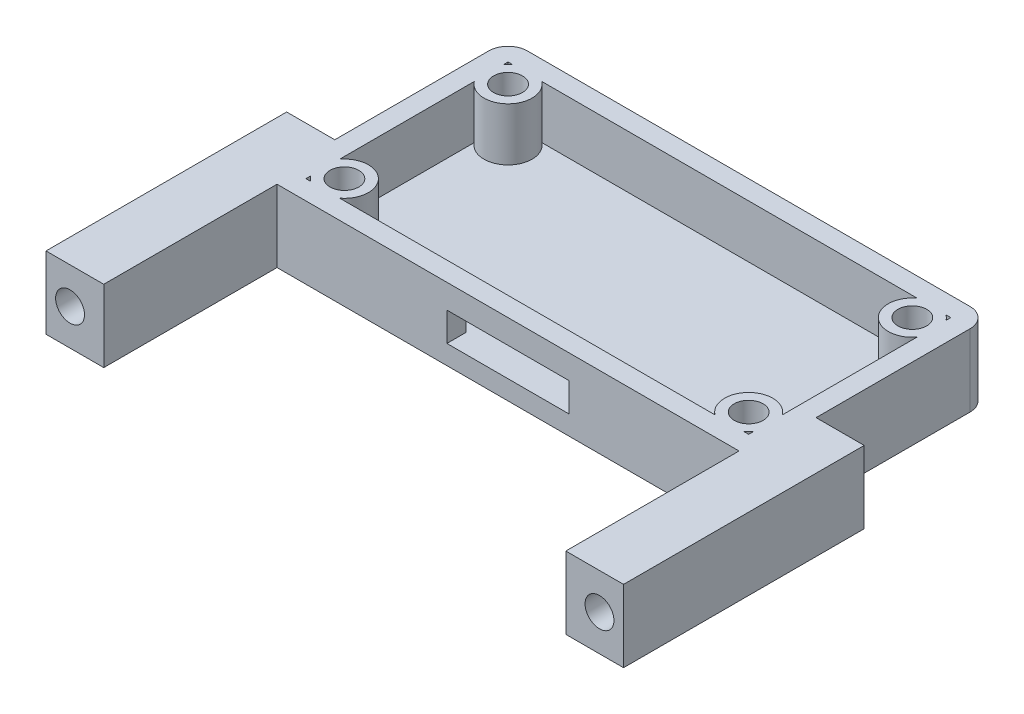
SolidWorks part; units mm, degrees
ref_plane "前视基准面" through (0, 0, 0) normal (0, 0, 1) x (1, 0, 0)
ref_plane "上视基准面" through (0, 0, 0) normal (0, 1, 0) x (1, 0, 0)
ref_plane "右视基准面" through (0, 0, 0) normal (1, 0, 0) x (0, 0, -1)
other "Configuration Table"
sketch "草图1" plane through (0, 0, 0) normal (0, 1, 0) x (1, 0, 0)
  line L1 (-23, 12.5) -> (23, 12.5)
  line L2 (-25, 10.5) -> (-25, -10.5)
  line L3 (-23, -12.5) -> (23, -12.5)
  line L4 (25, 10.5) -> (25, -10.5)
  line L5 (-25, 12.5) -> (25, -12.5) construction
  line L6 (-25, -12.5) -> (25, 12.5) construction
  arc A0 (-23, 12.5) -> (-25, 10.5) centre (-23, 10.5) ccw
  arc A1 (25, 10.5) -> (23, 12.5) centre (23, 10.5) ccw
  arc A2 (-25, -10.5) -> (-23, -12.5) centre (-23, -10.5) ccw
  arc A3 (23, -12.5) -> (25, -10.5) centre (23, -10.5) ccw
  point P0 (0, 0)
  dimension "D3" = 4
  dimension "D4" = 4
  dimension "D5" = 4
  dimension "D6" = 4
  dimension "D1" = 50
  dimension "D2" = 25
extrude "凸台-拉伸1" add sketch "草图1" along normal blind 2
sketch "草图2" plane through (0, 2, 0) normal (0, 1, 0) x (1, 0, 0)
  line L0 (-25, 10.5) -> (-25, -10.5) construction
  line L1 (-23, 10.5) -> (23, 10.5)
  line L2 (-23, 10.5) -> (-23, -10.5)
  line L3 (-23, -10.5) -> (23, -10.5)
  line L4 (23, 10.5) -> (23, -10.5)
  line L5 (-23, 10.5) -> (23, -10.5) construction
  line L6 (-23, -10.5) -> (23, 10.5) construction
  line L8 (23, 12.5) -> (-23, 12.5) construction
  line L13 (-25, 10.5) -> (-25, -10.5)
  line L14 (-23, -12.5) -> (23, -12.5)
  line L15 (25, -10.5) -> (25, 10.5)
  line L16 (23, 12.5) -> (-23, 12.5)
  line L17 (-25, 10.5) -> (-25, -10.5)
  line L18 (-23, -12.5) -> (23, -12.5)
  line L19 (25, -10.5) -> (25, 10.5)
  line L20 (23, 12.5) -> (-23, 12.5)
  arc A4 (-23, 12.5) -> (-25, 10.5) centre (-23, 10.5) ccw
  arc A5 (-25, -10.5) -> (-23, -12.5) centre (-23, -10.5) ccw
  arc A6 (23, -12.5) -> (25, -10.5) centre (23, -10.5) ccw
  arc A7 (25, 10.5) -> (23, 12.5) centre (23, 10.5) ccw
  arc A8 (-23, 12.5) -> (-25, 10.5) centre (-23, 10.5) ccw
  arc A9 (-25, -10.5) -> (-23, -12.5) centre (-23, -10.5) ccw
  arc A10 (23, -12.5) -> (25, -10.5) centre (23, -10.5) ccw
  arc A11 (25, 10.5) -> (23, 12.5) centre (23, 10.5) ccw
  point P0 (0, 0)
  dimension "D1" = 2
  dimension "D2" = 2
  dimension "D3" = 0
extrude "凸台-拉伸2" add sketch "草图2" along normal blind 5.5
sketch "草图3" plane through (0, 2, 0) normal (0, 1, 0) x (1, 0, 0)
  line L0 (-23, 10.5) -> (-23, -10.5) construction
  line L1 (23, 10.5) -> (-23, 10.5) construction
  line L2 (23, -10.5) -> (23, 10.5) construction
  line L3 (-23, 10.5) -> (-23, -10.5) construction
  line L6 (-23, -10.5) -> (23, -10.5) construction
  line L7 (23, -10.5) -> (23, 10.5) construction
  circle A0 centre (-21, 8.5) radius 1.5
  circle A1 centre (-21, -8.5) radius 1.5
  circle A2 centre (21, -8.5) radius 1.5
  circle A3 centre (21, 8.5) radius 1.5
  circle A4 centre (-21, 8.5) radius 2.5
  circle A5 centre (21, 8.5) radius 2.5
  circle A6 centre (21, -8.5) radius 2.5
  circle A7 centre (-21, -8.5) radius 2.5
  dimension "D1" = 3
  dimension "D2" = 3
  dimension "D3" = 3
  dimension "D4" = 3
  dimension "D6" = 2
  dimension "D7" = 2
  dimension "D8" = 2
  dimension "D13" = 5
  dimension "D14" = 5
  dimension "D15" = 5
  dimension "D16" = 5
  dimension "D5" = 2
  dimension "D9" = 2
  dimension "D10" = 2
  dimension "D11" = 2
  dimension "D12" = 2
extrude "凸台-拉伸3" add sketch "草图3" along normal blind 5.5
sketch "草图4" plane through (0, 7.5, 0) normal (0, 1, 0) x (1, 0, 0)
  line L0 (19.5, 10.5) -> (-19.5, 10.5) construction
  line L1 (-23, 7) -> (-23, -7) construction
  line L2 (-19.5, -10.5) -> (19.5, -10.5) construction
  line L3 (-23, 7) -> (-23, -7) construction
  line L4 (23, -7) -> (23, 7) construction
  line L5 (19.5, 10.5) -> (-19.5, 10.5) construction
  line L6 (23, -7) -> (23, 7) construction
  circle A8 centre (-21.5, 9) radius 1.5
  circle A9 centre (-21.5, -9) radius 1.5
  circle A10 centre (21.5, 9) radius 1.5
  circle A11 centre (21.5, -9) radius 1.5
  dimension "D1" = 3
  dimension "D2" = 3
  dimension "D3" = 3
  dimension "D4" = 3
  dimension "D7" = 1.5
  dimension "D9" = 1.5
  dimension "D10" = 1.5
  dimension "D11" = 1.5
  dimension "D12" = 1.5
  dimension "D5" = 1.5
  dimension "D6" = 1.5
  dimension "D8" = 1.5
sketch "草图5" plane through (0, 0, 12.5) normal (0, 0, 1) x (1, 0, 0)
  line L0 (-23, 0) -> (23, 0) construction
  line L1 (-6.35, 2) -> (6.35, 2)
  line L2 (-6.35, 2) -> (-6.35, 5)
  line L3 (-6.35, 5) -> (6.35, 5)
  line L4 (6.35, 2) -> (6.35, 5)
  dimension "D1" = 12.7
  dimension "D2" = 2
  dimension "D3" = 3
  dimension "D4" = 6.35
extrude "切除-拉伸2" cut sketch "草图5" against normal up to next
sketch "草图6" plane through (0, 0, 0) normal (0, -1, 0) x (1, 0, 0)
  line L0 (23, 12.5) -> (30, 12.5)
  line L1 (30, 12.5) -> (30, 10.5)
  line L2 (30, 10.5) -> (25, 10.5)
  line L3 (25, 10.5) -> (23, 12.5)
  line L4 (-23, 12.5) -> (-30, 12.5)
  line L5 (-30, 12.5) -> (-30, 10.5)
  line L6 (-30, 10.5) -> (-25, 10.5)
  line L7 (-25, 10.5) -> (-23, 12.5)
  dimension "D1" = 7
  dimension "D2" = 7
extrude "凸台-拉伸4" add sketch "草图6" against normal up to surface (7.5 mm away)
sketch "草图7" plane through (0, 0, 10.5) normal (0, 0, -1) x (-1, 0, 0)
  line L0 (-30, 7.5) -> (-30, 0) construction
  line L1 (-25, 7.5) -> (-30, 7.5) construction
  line L2 (30, 7.5) -> (25, 7.5) construction
  line L4 (30, 7.5) -> (30, 0) construction
  circle A0 centre (-27.5, 3.75) radius 1.5
  circle A1 centre (27.5, 3.75) radius 1.5
  dimension "D5" = 3
  dimension "D6" = 3
  dimension "D1" = 2.5
  dimension "D2" = 3.75
  dimension "D3" = 3.75
  dimension "D4" = 2.5
extrude "切除-拉伸3" cut sketch "草图7" against normal through all
sketch "草图8" plane through (0, 0, 12.5) normal (0, 0, 1) x (1, 0, 0)
  line L0 (-29, 7.5) -> (-29, 3.75)
  line L1 (29, 7.5) -> (29, 3.75)
  line L2 (-26, 7.5) -> (-26, 3.75)
  line L3 (26, 7.5) -> (26, 3.75)
  line L4 (-30, 0) -> (30, 0)
  line L5 (30, 0) -> (30, 7.5)
  line L6 (30, 7.5) -> (-30, 7.5)
  line L7 (-30, 7.5) -> (-30, 0)
  line L8 (-30, 0) -> (-24, 0)
  line L9 (30, 0) -> (30, 7.5)
  line L10 (30, 7.5) -> (29, 7.5)
  line L11 (-30, 7.5) -> (-30, 0)
  line L12 (-24, 7.5) -> (-24, 0)
  line L13 (24, 7.5) -> (24, 0)
  line L14 (-29, 7.5) -> (-30, 7.5)
  line L15 (26, 7.5) -> (24, 7.5)
  line L16 (-24, 7.5) -> (-26, 7.5)
  line L17 (24, 0) -> (30, 0)
  circle A0 centre (-27.5, 3.75) radius 1.5 construction
  circle A1 centre (27.5, 3.75) radius 1.5 construction
  arc A2 (-29, 3.75) -> (-26, 3.75) centre (-27.5, 3.75) ccw
  arc A3 (26, 3.75) -> (29, 3.75) centre (27.5, 3.75) ccw
  dimension "D2" = 2
  dimension "D3" = 2
  dimension "D1" = 0
extrude "凸台-拉伸5" add sketch "草图8" along normal blind 18
sketch "草图9" plane through (0, 0, 12.5) normal (0, 0, 1) x (1, 0, 0)
  line L3 (29, 3.75) -> (29, 7.5)
  line L4 (29, 7.5) -> (26, 7.5)
  line L5 (26, 7.5) -> (26, 3.75)
  line L6 (29, 3.75) -> (29, 7.5)
  line L7 (29, 7.5) -> (26, 7.5)
  line L8 (26, 7.5) -> (26, 3.75)
  line L9 (-29, 7.5) -> (-29, 3.75)
  line L10 (-26, 3.75) -> (-26, 7.5)
  line L11 (-26, 7.5) -> (-29, 7.5)
  line L12 (-29, 7.5) -> (-29, 3.75)
  line L13 (-26, 3.75) -> (-26, 7.5)
  line L14 (-26, 7.5) -> (-29, 7.5)
  arc A1 (29, 3.75) -> (26, 3.75) centre (27.5, 3.75) ccw
  arc A2 (29, 3.75) -> (26, 3.75) centre (27.5, 3.75) ccw
  arc A3 (-26, 3.75) -> (-29, 3.75) centre (-27.5, 3.75) ccw
  arc A4 (-26, 3.75) -> (-29, 3.75) centre (-27.5, 3.75) ccw
  dimension "D1" = 0
  dimension "D2" = 0
extrude "凸台-拉伸6" add sketch "草图9" along normal up to surface (18 mm away) up to face at (-27.25, 4.5, 30.5)
sketch "草图10" plane through (0, 0, 10.5) normal (0, 0, -1) x (-1, 0, 0)
  line L4 (-25, 0) -> (-25, 7.5)
  line L5 (-25, 7.5) -> (-30, 7.5)
  line L6 (-30, 7.5) -> (-30, 0)
  line L7 (-30, 0) -> (-25, 0)
  line L8 (-25, 0) -> (-25, 7.5)
  line L9 (-25, 7.5) -> (-30, 7.5)
  line L10 (-30, 7.5) -> (-30, 0)
  line L11 (-30, 0) -> (-25, 0)
  line L12 (30, 0) -> (30, 7.5)
  line L13 (30, 7.5) -> (25, 7.5)
  line L14 (25, 7.5) -> (25, 0)
  line L15 (25, 0) -> (30, 0)
  line L16 (30, 0) -> (30, 7.5)
  line L17 (30, 7.5) -> (25, 7.5)
  line L18 (25, 7.5) -> (25, 0)
  line L19 (25, 0) -> (30, 0)
  circle A0 centre (-27.5, 3.75) radius 1.5 construction
  circle A1 centre (-27.5, 3.75) radius 1.5
  circle A2 centre (27.5, 3.75) radius 1.5 construction
  circle A3 centre (27.5, 3.75) radius 1.5
  dimension "D1" = 0
  dimension "D2" = 0
extrude "凸台-拉伸7" add sketch "草图10" along normal blind 5
